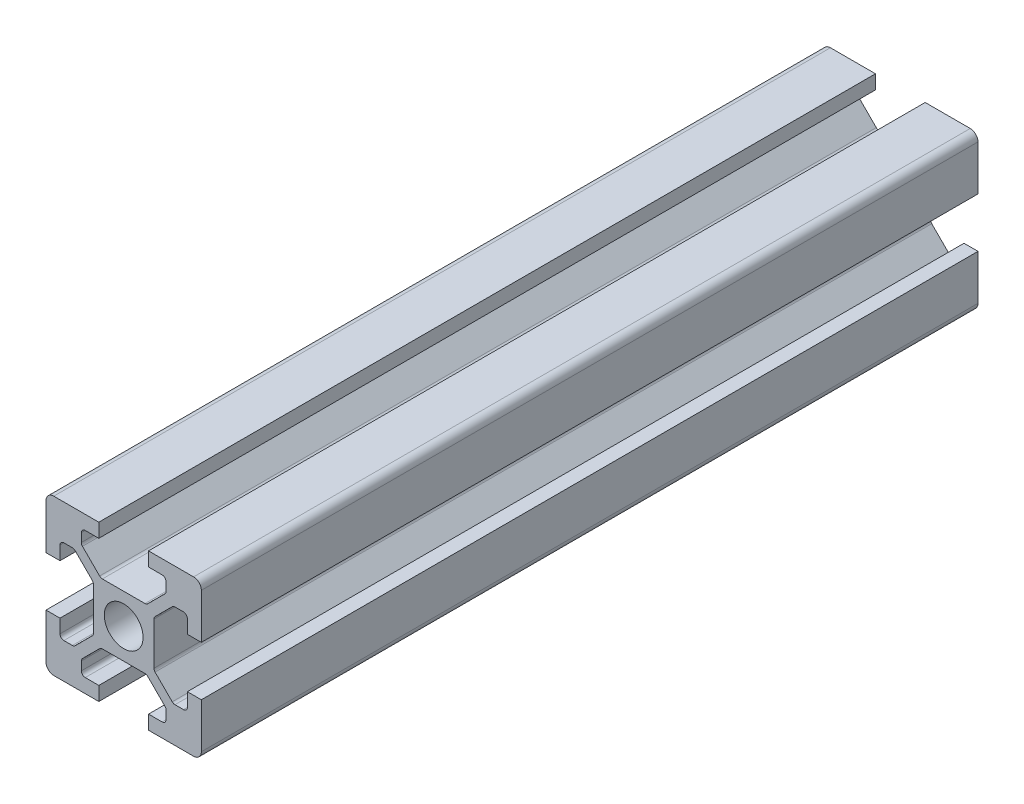
SolidWorks part; units mm, degrees
material "1060 Alloy"
ref_plane "Front Plane" through (0, 0, 0) normal (0, 0, 1) x (1, 0, 0)
ref_plane "Top Plane" through (0, 0, 0) normal (0, 1, 0) x (1, 0, 0)
ref_plane "Right Plane" through (0, 0, 0) normal (1, 0, 0) x (0, 0, -1)
sketch "Sketch1" plane through (0, 0, 0) normal (0, 0, 1) x (1, 0, 0)
  line L0 (20, 0) -> (-8.059, 28.059) construction
  line L1 (0, 0) -> (6.8, 0)
  line L2 (0, 0) -> (0, 6.8)
  line L3 (0, 20) -> (6.8, 20)
  line L4 (20, 0) -> (20, 6.8)
  line L5 (6.8, 20) -> (6.8, 18.2)
  line L6 (20, 20) -> (8.2322, 8.2322) construction
  line L7 (12.95, 6.1) -> (7.05, 6.1)
  line L8 (13.9, 7.05) -> (13.9, 12.95)
  line L9 (12.95, 13.9) -> (7.05, 13.9)
  line L10 (6.1, 7.05) -> (6.1, 12.95)
  line L11 (13.9, 6.1) -> (6.1, 13.9) construction
  line L12 (13.9, 13.9) -> (6.1, 6.1) construction
  line L13 (4.55, 16.4) -> (7.05, 13.9)
  line L14 (13.2, 18.2) -> (13.2, 20)
  line L15 (1.8, 6.8) -> (0, 6.8)
  line L16 (0, 13.2) -> (0, 20)
  line L17 (0, 13.2) -> (1.8, 13.2)
  line L18 (10, 10) -> (10, 13.9) construction
  line L19 (16.4, 4.55) -> (13.9, 7.05)
  line L20 (4.55, 16.4) -> (4.55, 18.2)
  line L21 (4.55, 18.2) -> (6.8, 18.2)
  line L22 (13.2, 18.2) -> (15.45, 18.2)
  line L23 (15.45, 18.2) -> (15.45, 16.4)
  line L24 (15.45, 16.4) -> (12.95, 13.9)
  line L25 (16.4, 4.55) -> (18.2, 4.55)
  line L26 (18.2, 4.55) -> (18.2, 6.8)
  line L27 (20, 6.8) -> (18.2, 6.8)
  line L28 (18.2, 13.2) -> (20, 13.2)
  line L29 (18.2, 13.2) -> (18.2, 15.45)
  line L30 (18.2, 15.45) -> (16.4, 15.45)
  line L31 (16.4, 15.45) -> (13.9, 12.95)
  line L32 (1.8, 4.55) -> (3.6, 4.55)
  line L33 (3.6, 15.45) -> (6.1, 12.95)
  line L34 (3.6, 15.45) -> (1.8, 15.45)
  line L35 (1.8, 15.45) -> (1.8, 13.2)
  line L38 (3.6, 4.55) -> (6.1, 7.05)
  line L39 (1.8, 6.8) -> (1.8, 4.55)
  line L40 (15.45, 3.6) -> (12.95, 6.1)
  line L41 (4.55, 3.6) -> (7.05, 6.1)
  line L42 (4.55, 1.8) -> (4.55, 3.6)
  line L43 (6.8, 1.8) -> (4.55, 1.8)
  line L44 (6.8, 1.8) -> (6.8, 0)
  line L45 (15.45, 3.6) -> (15.45, 1.8)
  line L46 (15.45, 1.8) -> (13.2, 1.8)
  line L47 (13.2, 0) -> (13.2, 1.8)
  line L48 (13.2, 20) -> (20, 20)
  line L49 (20, 13.2) -> (20, 20)
  line L50 (13.2, 0) -> (20, 0)
  line L51 (6.1, 6.1) -> (-5.5045, -5.5045) construction
  circle A0 centre (10, 10) radius 2.5
  point P25 (10, 16.4)
  point P39 (13.2, 19.1)
  point P46 (0.9, 6.8)
  dimension "D3" = 5
  dimension "D2" = 20
  dimension "D4" = 7.8
  dimension "D5" = 7.8
  dimension "D6" = 6.8
  dimension "D7" = 6.8
  dimension "D8" = 1.8
  dimension "D9" = 10.9
  dimension "D10" = 1.8
  dimension "D11" = 10.9
  dimension "D12" = 20
extrude "Boss-Extrude1" add sketch "Sketch1" along normal blind 300 contours L47 L50 L4 L27 L26 L25 L19 L8 L31 L30 L29 L28 L49 L48 L14 L22 L23 L24 L9 L13 L20 L21 L5 L3 L16 L17 L35 L34 L33 L10 L38 L32 L39 L15 L2 L1 L44 L43 L42 L41 L7 L40 L45 L46 A0
fillet "Fillet1" radius 1 4 edges at (20, 20, 150) (20, 0, 150) (0, 0, 150) (0, 20, 150)
fillet "Fillet2" radius 0.5 6 edges at (4.55, 18.2, 150) (4.55, 16.4, 150) (7.05, 13.9, 150) (15.45, 18.2, 150) (15.45, 16.4, 150) (12.95, 13.9, 150)
fillet "Fillet3" radius 0.5 6 edges at (18.2, 15.45, 150) (16.4, 15.45, 150) (13.9, 12.95, 150) (18.2, 4.55, 150) (13.9, 7.05, 150) (16.4, 4.55, 150)
fillet "Fillet4" radius 0.5 6 edges at (1.8, 15.45, 150) (3.6, 15.45, 150) (6.1, 12.95, 150) (3.6, 4.55, 150) (1.8, 4.55, 150) (6.1, 7.05, 150)
fillet "Fillet5" radius 0.5 6 edges at (7.05, 6.1, 150) (4.55, 3.6, 150) (4.55, 1.8, 150) (15.45, 1.8, 150) (15.45, 3.6, 150) (12.95, 6.1, 150)
sketch "Sketch4" plane through (0, 0, 0) normal (0, 0, -1) x (-1, 0, 0)
  line L1 (55.7447, -48.755) -> (-29.3857, -48.755)
  line L2 (55.7447, -48.755) -> (55.7447, 27.7374)
  line L3 (55.7447, 27.7374) -> (-29.3857, 27.7374)
  line L4 (-29.3857, -48.755) -> (-29.3857, 27.7374)
  line L5 (55.7447, -48.755) -> (-29.3857, 27.7374) construction
  line L6 (55.7447, 27.7374) -> (-29.3857, -48.755) construction
  point P0 (13.1795, -10.5088)
extrude "Cut-Extrude4" cut sketch "Sketch4" against normal blind 200
